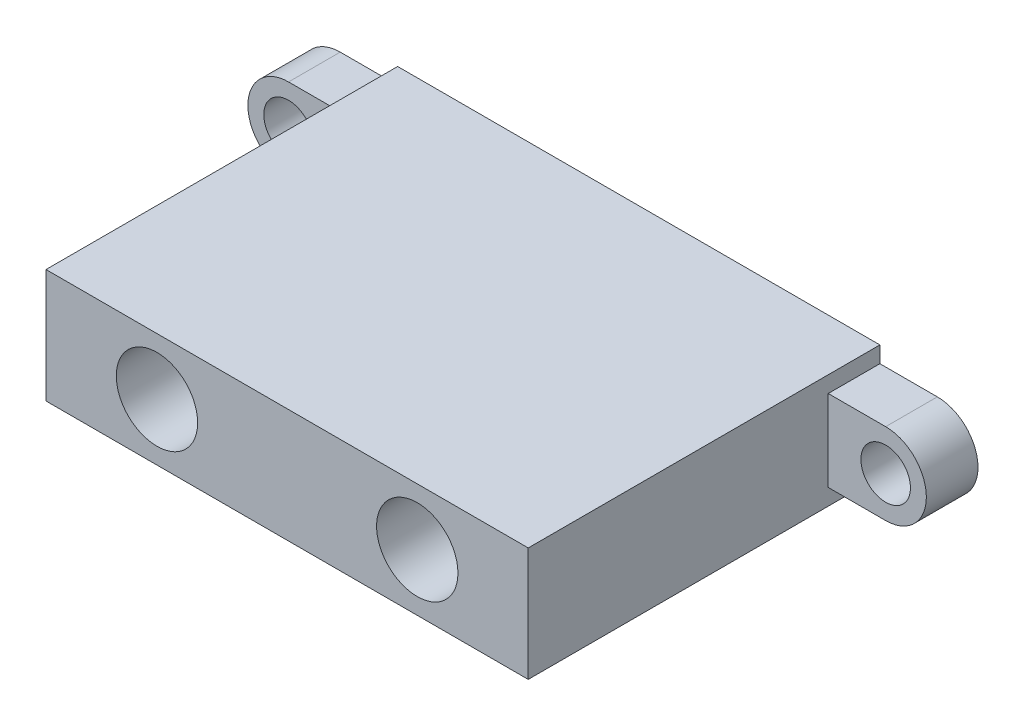
SolidWorks part; units mm, degrees
ref_plane "Front" through (0, 0, 0) normal (0, 0, 1) x (1, 0, 0)
ref_plane "Top" through (0, 0, 0) normal (0, 1, 0) x (1, 0, 0)
ref_plane "Right" through (0, 0, 0) normal (1, 0, 0) x (0, 0, -1)
sketch "Sketch1" plane through (0, 0, 0) normal (0, 0, 1) x (1, 0, 0)
  line L1 (0, 0) -> (29.6418, 0)
  line L2 (0, 0) -> (0, 7)
  line L3 (0, 7) -> (29.6418, 7)
  line L4 (29.6418, 0) -> (29.6418, 7)
  dimension "D1" = 29.6418
  dimension "D2" = 7
extrude "Boss-Extrude1" add sketch "Sketch1" along normal blind 21.6154
sketch "Sketch2" plane through (0, 0, 0) normal (0, 0, -1) x (-1, 0, 0)
  line L0 (-33.1724, 3.5) -> (3.5306, 3.5) construction
  line L1 (-33.1724, 6) -> (3.5306, 6)
  line L2 (-33.1724, 1) -> (3.5306, 1)
  line L3 (-29.6418, 0) -> (-29.6418, 7) construction
  line L4 (-29.6418, 7) -> (0, 7) construction
  arc A0 (-33.1724, 6) -> (-33.1724, 1) centre (-33.1724, 3.5) ccw
  arc A1 (3.5306, 1) -> (3.5306, 6) centre (3.5306, 3.5) ccw
  circle A2 centre (-33.1724, 3.5) radius 1.524
  circle A3 centre (3.5306, 3.5) radius 1.524
  point P2 (-14.8209, 3.5)
  point P9 (-29.6418, 3.5)
  point P12 (-14.8209, 7)
  point P17 (0, 0)
  dimension "D2" = 3.048
  dimension "D1" = 36.703
  dimension "D3" = 5
extrude "Boss-Extrude2" add sketch "Sketch2" against normal blind 3.175
sketch "Sketch3" plane through (0, 0, 21.6154) normal (0, 0, 1) x (1, 0, 0)
  line L0 (0, 7) -> (0, 0) construction
  line L1 (6.8209, 3.5) -> (22.8209, 3.5) construction
  line L2 (29.6418, 7) -> (0, 7) construction
  circle A0 centre (6.8209, 3.5) radius 2.5
  circle A1 centre (22.8209, 3.5) radius 2.5
  point P7 (0, 3.5)
  point P9 (14.8209, 7)
  point P10 (14.8209, 3.5)
  dimension "D1" = 5
  dimension "D2" = 16
extrude "Cut-Extrude1" cut sketch "Sketch3" against normal blind 3.81
